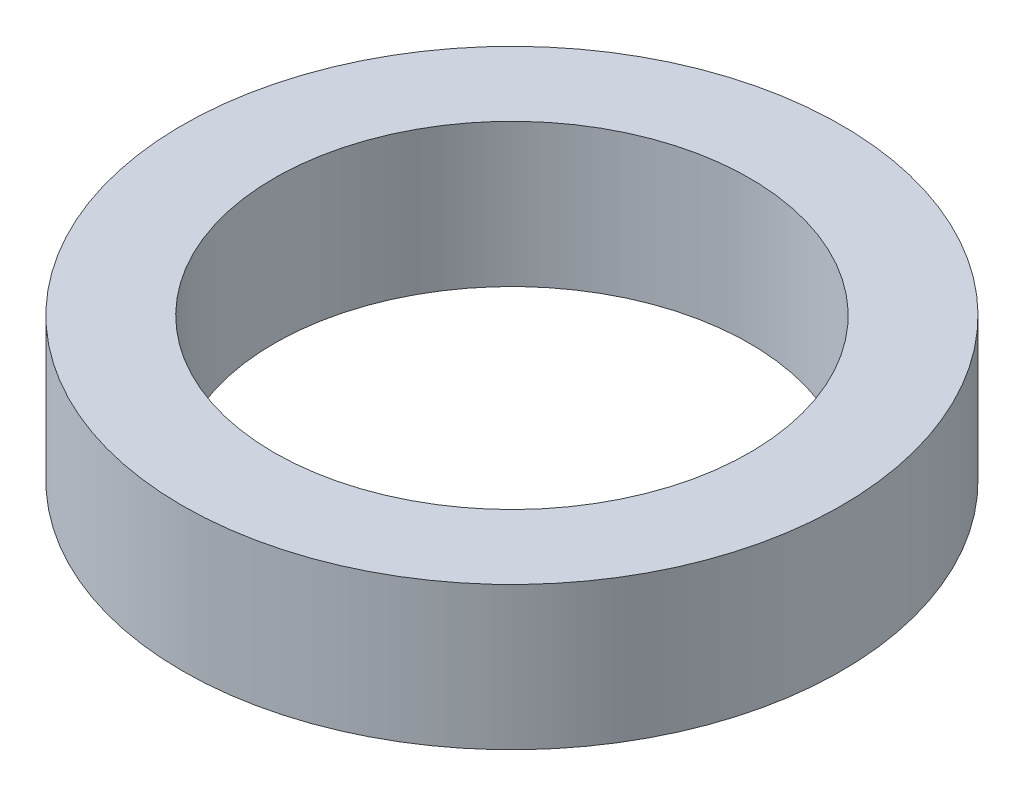
SolidWorks part; units mm, degrees
ref_plane "Front Plane" through (0, 0, 0) normal (0, 0, 1) x (1, 0, 0)
ref_plane "Top Plane" through (0, 0, 0) normal (0, 1, 0) x (1, 0, 0)
ref_plane "Right Plane" through (0, 0, 0) normal (1, 0, 0) x (0, 0, -1)
sketch "Sketch1" plane through (0, 0, 0) normal (0, 1, 0) x (1, 0, 0)
  circle A0 centre (0, 0) radius 3.5
  circle A1 centre (0, 0) radius 2.525
  dimension "D1" = 7
  dimension "D2" = 5.05
extrude "Boss-Extrude1" add sketch "Sketch1" along normal blind 1.52
